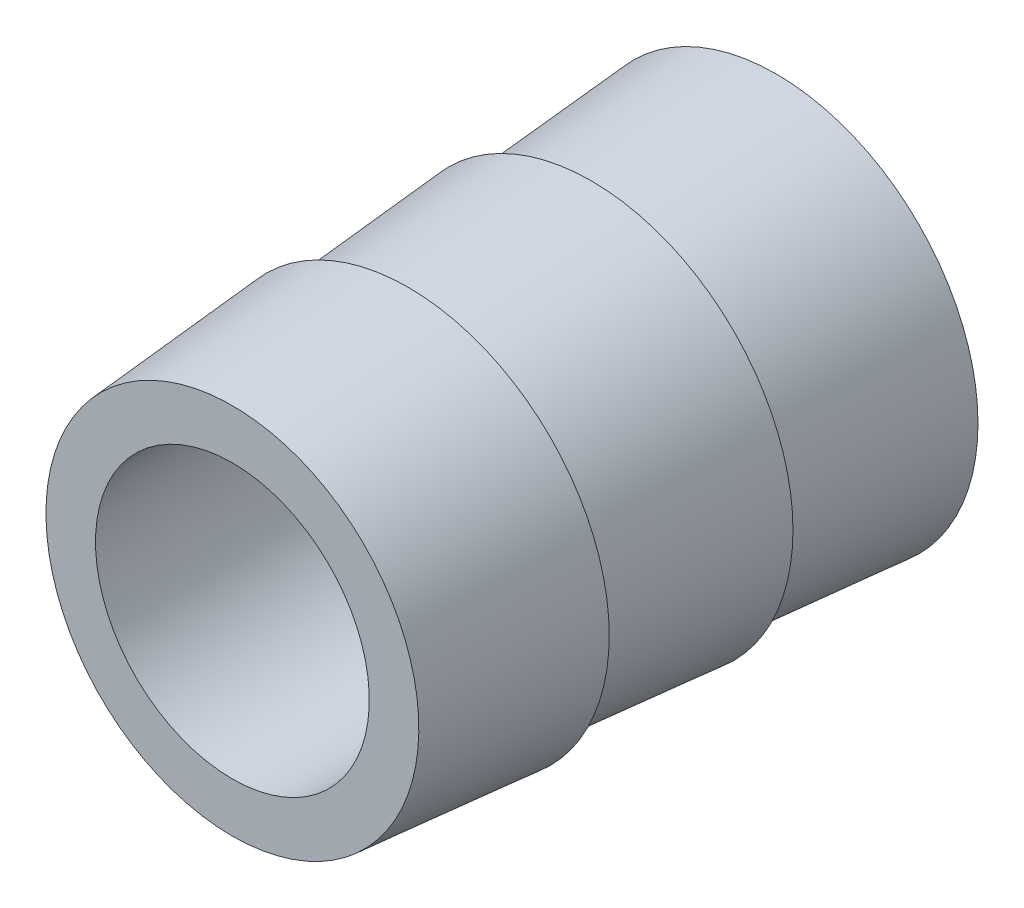
SolidWorks part; units mm, degrees
ref_plane "Front Plane" through (0, 0, 0) normal (0, 0, 1) x (1, 0, 0)
ref_plane "Top Plane" through (0, 0, 0) normal (0, 1, 0) x (1, 0, 0)
ref_plane "Right Plane" through (0, 0, 0) normal (1, 0, 0) x (0, 0, -1)
sketch "Sketch2" plane through (0, 0, 0) normal (1, 0, 0) x (0, 0, -1)
  line L0 (-0.5417, -1.2698) -> (6.8513, -1.2698)
  line L4 (-4.2206, 0.9631) -> (-0.5417, 1.2671) construction
  line L5 (-0.5417, 1.2671) -> (-0.5417, 2.475)
  line L7 (3.1371, 1.279) -> (3.1371, 2.4869)
  line L9 (6.8513, 1.2818) -> (6.8513, -1.2698)
  line L10 (-4.2206, 0.9631) -> (-4.0749, 0.9751)
  line L13 (-4.0749, 0.9751) -> (-4.0749, -1.2698)
  line L14 (-0.5417, 0.975) -> (-0.5417, -1.2698) construction
  line L15 (-0.5417, -1.2698) -> (-4.0749, -1.2698)
  line L16 (6.8513, 1.2818) -> (3.1371, 0.9869) construction
  line L17 (3.1371, 1.279) -> (-0.5417, 0.975) construction
  line L18 (3.1371, 1.279) -> (3.1371, 2.779)
  line L19 (3.1371, 2.779) -> (-0.5417, 2.475)
  line L21 (6.8513, 1.2818) -> (6.8513, 2.7818)
  line L22 (6.8513, 2.7818) -> (3.1371, 2.4869)
  line L23 (3.1371, 2.4869) -> (3.1371, 0.9869) construction
  line L24 (-0.5417, 1.2671) -> (-0.5417, 1.7692) construction
  line L25 (-0.5417, 1.2671) -> (-0.5417, 0.975)
  line L26 (-4.0749, 0.9751) -> (-4.0749, 2.4751)
  line L27 (-0.5417, 1.2671) -> (-0.5417, 2.7671)
  line L28 (-0.5417, 2.7671) -> (-4.0749, 2.4751)
  dimension "D1" = 1.5
  dimension "D2" = 1.5
  dimension "D3" = 1.5
revolve "Revolve2" add sketch "Sketch2" angle 360 about L0
sketch "Sketch7" plane through (0, 0, -6.8513) normal (0, 0, -1) x (-1, 0, 0)
  line L0 (0, 2.7818) -> (0, -5.3215) construction
  circle A0 centre (0, -1.2698) radius 4.0516 construction
  circle A1 centre (0, -1.2698) radius 2.75
  dimension "D1" = 5.5
extrude "Cut-Extrude3" cut sketch "Sketch7" against normal through all
